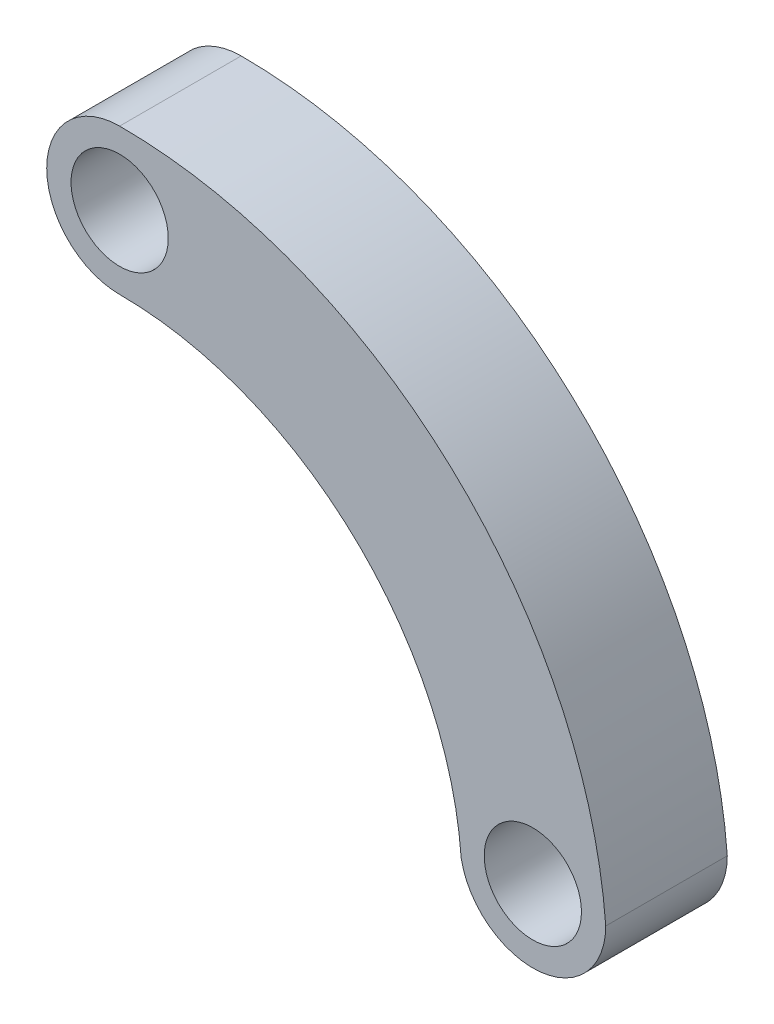
SolidWorks part; units mm, degrees
ref_plane "Alzado" through (0, 0, 0) normal (0, 0, 1) x (1, 0, 0)
ref_plane "Planta" through (0, 0, 0) normal (0, 1, 0) x (1, 0, 0)
ref_plane "Vista lateral" through (0, 0, 0) normal (1, 0, 0) x (0, 0, -1)
sketch "Croquis1" plane through (0, 0, 0) normal (0, 0, 1) x (1, 0, 0)
  line L0 (0, 20) -> (0, 30) construction
  line L1 (0, -20) -> (0, -30) construction
  line L2 (0, -30) -> (0, -155) construction
  line L3 (0, -155) -> (200, -155) construction
  line L4 (200, -155) -> (200, -180.8454) construction
  line L5 (200, -180.8454) -> (140, -180.8454) construction
  line L7 (0, -155) -> (-200, -155) construction
  line L8 (-200, -155) -> (-200, -113.1841) construction
  line L9 (-200, -113.1841) -> (-140, -113.1841) construction
  line L10 (-140, -113.1841) -> (-140, -155) construction
  circle A0 centre (0, 0) radius 20
  arc A1 (0, 30) -> (0, -30) centre (0, 0) ccw
  arc A2 (140.5203, -160.5631) -> (200, -155) centre (170, -155) ccw
  arc A3 (200, -155) -> (0, 30) centre (0, -170.6081) ccw
  arc A4 (-192.2137, -113.1841) -> (-200, -155) centre (0, -170.6081) ccw
  arc A5 (140.5203, -160.5631) -> (0, -30) centre (0, -170.9) ccw
  circle A6 centre (170, -155) radius 20
  dimension "D1" = 40
  dimension "D7" = 40
  dimension "D2" = 10
  dimension "D3" = 125
  dimension "D4" = 200
  dimension "D5" = 60
  dimension "D6" = 60
extrude "Saliente-Extruir1" add sketch "Croquis1" along normal blind 50 contours A5 A2 A3 A1 A6 A0
